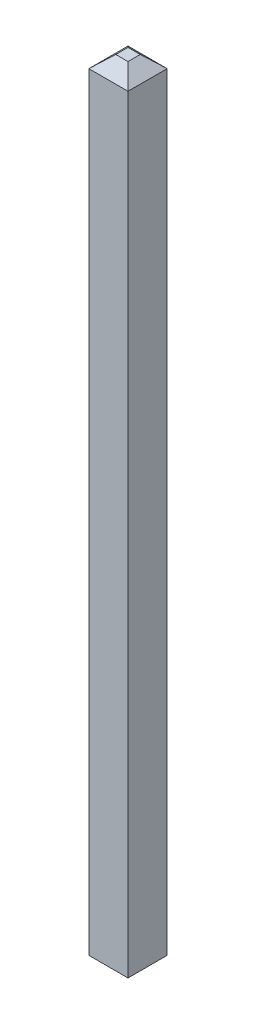
SolidWorks part; units mm, degrees
ref_plane "Front Plane" through (0, 0, 0) normal (0, 0, 1) x (1, 0, 0)
ref_plane "Top Plane" through (0, 0, 0) normal (0, 1, 0) x (1, 0, 0)
ref_plane "Right Plane" through (0, 0, 0) normal (1, 0, 0) x (0, 0, -1)
sketch "Sketch1" plane through (0, 0, 0) normal (0, 1, 0) x (1, 0, 0)
  line L1 (-0.32, 0.32) -> (0.32, 0.32)
  line L2 (-0.32, 0.32) -> (-0.32, -0.32)
  line L3 (-0.32, -0.32) -> (0.32, -0.32)
  line L4 (0.32, 0.32) -> (0.32, -0.32)
  line L5 (-0.32, 0.32) -> (0.32, -0.32) construction
  line L6 (-0.32, -0.32) -> (0.32, 0.32) construction
  point P0 (0, 0)
  dimension "D1" = 0.64
  dimension "D2" = 0.64
extrude "Boss-Extrude1" add sketch "Sketch1" along normal blind 12.54
ref_plane "Plane1" through (0, 12.74, 0) normal (0, 1, 0) x (1, 0, 0)
sketch "Sketch3" plane through (0, 12.74, 0) normal (0, 1, 0) x (1, 0, 0)
  line L1 (0.1, 0.1) -> (-0.1, 0.1)
  line L2 (0.1, 0.1) -> (0.1, -0.1)
  line L3 (0.1, -0.1) -> (-0.1, -0.1)
  line L4 (-0.1, 0.1) -> (-0.1, -0.1)
  line L5 (0.1, 0.1) -> (-0.1, -0.1) construction
  line L6 (0.1, -0.1) -> (-0.1, 0.1) construction
  point P0 (0, 0)
  dimension "D1" = 0.2
  dimension "D2" = 0.2
loft "Loft1" add profiles "Sketch3" section "Sketch3" section face at (0, 12.54, 0)
ref_plane "Plane2" through (0, -0.2, 0) normal (0, -1, 0) x (-1, 0, 0)
sketch "Sketch4" plane through (0, -0.2, 0) normal (0, -1, 0) x (-1, 0, 0)
  line L1 (0.1, 0.1) -> (-0.1, 0.1)
  line L2 (0.1, 0.1) -> (0.1, -0.1)
  line L3 (0.1, -0.1) -> (-0.1, -0.1)
  line L4 (-0.1, 0.1) -> (-0.1, -0.1)
  line L5 (0.1, 0.1) -> (-0.1, -0.1) construction
  line L6 (0.1, -0.1) -> (-0.1, 0.1) construction
  point P0 (0, 0)
  dimension "D1" = 0.2
  dimension "D2" = 0.2
loft "Loft2" add profiles "Sketch4" section "Sketch4" section face at (0, 0, 0)
